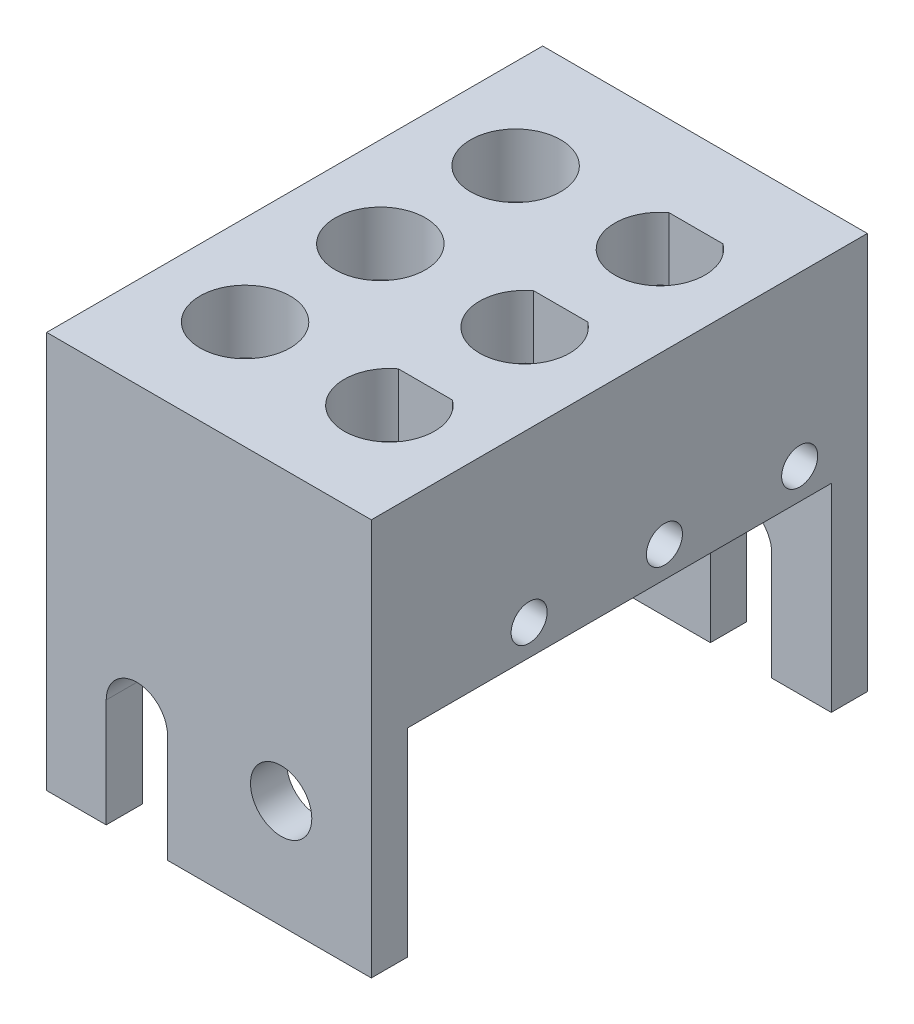
SolidWorks part; units mm, degrees
ref_plane "Спереди" through (0, 0, 0) normal (0, 0, 1) x (1, 0, 0)
ref_plane "Сверху" through (0, 0, 0) normal (0, 1, 0) x (1, 0, 0)
ref_plane "Справа" through (0, 0, 0) normal (1, 0, 0) x (0, 0, -1)
sketch "Эскиз1" plane through (0, 0, 0) normal (0, 1, 0) x (1, 0, 0)
  line L0 (-4, 13.75) -> (-4, 7.25) construction
  line L1 (-9, 13.75) -> (9, 13.75)
  line L2 (-9, 13.75) -> (-9, -13.75)
  line L3 (-9, -13.75) -> (9, -13.75)
  line L4 (9, 13.75) -> (9, -13.75)
  line L5 (0, -13.75) -> (0, 13.75) construction
  line L6 (-9, 0) -> (9, 0) construction
  line L7 (-4, 7.25) -> (-9, 7.25) construction
  line L8 (-4, 7.25) -> (-4, -0.25) construction
  line L9 (-4, -0.25) -> (-4, -7.75) construction
  line L10 (4, 9.75) -> (4, 9.25) construction
  line L11 (2.5, 9.25) -> (5.5, 9.25)
  line L12 (2.5, 1.75) -> (5.5, 1.75)
  line L13 (2.5, -5.75) -> (5.5, -5.75)
  circle A0 centre (-4, 7.25) radius 2.5
  circle A1 centre (-4, -0.25) radius 2.5
  arc A4 (5.5, 1.75) -> (2.5, 1.75) centre (4, -0.25) cw
  arc A5 (5.5, 9.25) -> (2.5, 9.25) centre (4, 7.25) cw
  circle A6 centre (-4, -7.75) radius 2.5
  arc A7 (5.5, -5.75) -> (2.5, -5.75) centre (4, -7.75) cw
  arc A8 (2.5, 9.25) -> (5.5, 9.25) centre (4, 7.25) cw construction
  point P0 (0, 0)
  dimension "D7" = 5
  dimension "D8" = 5
  dimension "D9" = 5
  dimension "D1" = 27.5
  dimension "D2" = 18
  dimension "D3" = 6.5
  dimension "D4" = 5
  dimension "D5" = 7.5
  dimension "D6" = 7.5
  dimension "D10" = 0.5
  dimension "D11" = 3
extrude "top-surface" add sketch "Эскиз1" against normal blind 3.5 contours L1 L4 L3 L2
sketch "Эскиз2" plane through (0, 0, 13.75) normal (0, 0, 1) x (1, 0, 0)
  line L0 (9, -3.5) -> (9, 0) construction
  line L1 (-9, 0) -> (9, 0)
  line L2 (-9, 0) -> (-9, -22)
  line L3 (-9, -22) -> (9, -22)
  line L4 (9, 0) -> (9, -22)
  line L5 (-9, -16) -> (-4, -16) construction
  line L6 (-4, -16) -> (-4, -22) construction
  line L7 (-5.7, -16) -> (-5.7, -22)
  line L8 (-2.3, -16) -> (-2.3, -22)
  line L9 (0, 0) -> (0, -22) construction
  line L10 (-4, 0) -> (-4, -14.5) construction
  line L11 (-4, -14.5) -> (-4, -16) construction
  arc A0 (-2.3, -16) -> (-5.7, -16) centre (-4, -16) ccw
  circle A1 centre (4, -16) radius 1.7
  line M11 (-9, -3.5) -> (9, -3.5)
  dimension "D4" = 3.4
  dimension "D1" = 5
  dimension "D2" = 6
  dimension "D3" = 22
  dimension "D5" = 14.5
  dimension "D6" = 1.5
extrude "front-wall" add sketch "Эскиз2" against normal blind 2 contours A0 L8 L3 L4 L2 L7 A1 M11
sketch "pivot" plane through (0, 0, 0) normal (0, 0, 1) x (1, 0, 0)
  line L0 (0, 0) -> (0, 18.5011) construction
pattern_circular "Круговой массив1" count 2 every 180 about axis through (0, 0, 0) along (0, 1, 0) of "front-wall"
sketch "Эскиз4" plane through (-9, 0, 0) normal (-1, 0, 0) x (0, 0, 1)
  line L0 (-11.75, -9.3) -> (-6.25, -9.3) construction
  line L1 (-11.75, -3.5) -> (-11.75, -22) construction
  line L2 (-6.25, -9.3) -> (-3.75, -9.3) construction
  line L3 (-11.75, -9.3) -> (-11.75, 0) construction
  line L4 (-13.75, 0) -> (13.75, 0) construction
  circle A0 centre (-5, -9.3) radius 1
  circle A2 centre (2.5, -9.3) radius 1
  circle A3 centre (10, -9.3) radius 1
  dimension "D3" = 2
  dimension "D1" = 5.5
  dimension "D2" = 2.5
  dimension "D5" = 9.3
  dimension "D4" = 3
sketch "Эскиз5" plane through (0, 0, 13.75) normal (0, 0, 1) x (1, 0, 0)
  line L1 (-9, -22) -> (-9, 0) construction
  line L2 (-9, -11) -> (-7, -11)
  line L3 (-7, -7.6) -> (-7, -1.5)
  line L4 (-7, -1.5) -> (-1, -1.5)
  line L5 (-1, -1.5) -> (-1, -7.6)
  line L6 (-1, -11) -> (0, -11)
  line L7 (0, -11) -> (0, -1.5)
  line L8 (-9, 0) -> (9, 0) construction
  line L10 (-7, 0) -> (-7, -1.5) construction
  line L11 (-9, -11) -> (-9, -1.5)
  line L12 (-9, -1.5) -> (-7, -1.5)
  line L13 (-1, -1.5) -> (0, -1.5)
  line L14 (0, -1.5) -> (0, 0) construction
  line L15 (-7, -11) -> (-6.3, -10.3)
  line L16 (-6.3, -10.3) -> (-6.3, -8.3)
  line L17 (-6.3, -8.3) -> (-7, -7.6)
  line L18 (-4, -1.5) -> (-4, 0) construction
  line L19 (-7, -7.6) -> (-7, -11) construction
  line L20 (-7, -9.3) -> (-6.3, -9.3) construction
  line L21 (-1, -11) -> (-1.7, -10.3)
  line L22 (-1.7, -10.3) -> (-1.7, -8.3)
  line L23 (-1.7, -8.3) -> (-1, -7.6)
  line L24 (-1, -1.5) -> (0, -1.5)
  point P22 (-1.0176, -10.9824)
  line M14 (-9, 0) -> (-9, -22)
  dimension "D1" = 2
  dimension "D2" = 1.5
  dimension "D3" = 6
  dimension "D4" = 9.5
  dimension "D5" = 1
  dimension "D6" = 2
  dimension "D7" = 45
  dimension "D8" = 45
  dimension "D9" = 0.7
extrude "side-rails" add sketch "Эскиз5" against normal blind 27.5 contours L16 L17 L3 L12 L2 L15 M14 | L23 L22 L21 L6 L7 L13 L5
extrude "separators-cutouts" cut sketch "Эскиз4" against normal blind 9
pattern_circular "Круговой массив5" count 2 every 180 about axis through (0, 0, 0) along (0, 1, 0) of "side-rails", "separators-cutouts"
equation "\"opening_diam\"= 5мм"
equation "\"D7@Эскиз1\"=\"opening_diam\""
equation "\"D8@Эскиз1\"=\"opening_diam\""
equation "\"D9@Эскиз1\"=\"opening_diam\""
